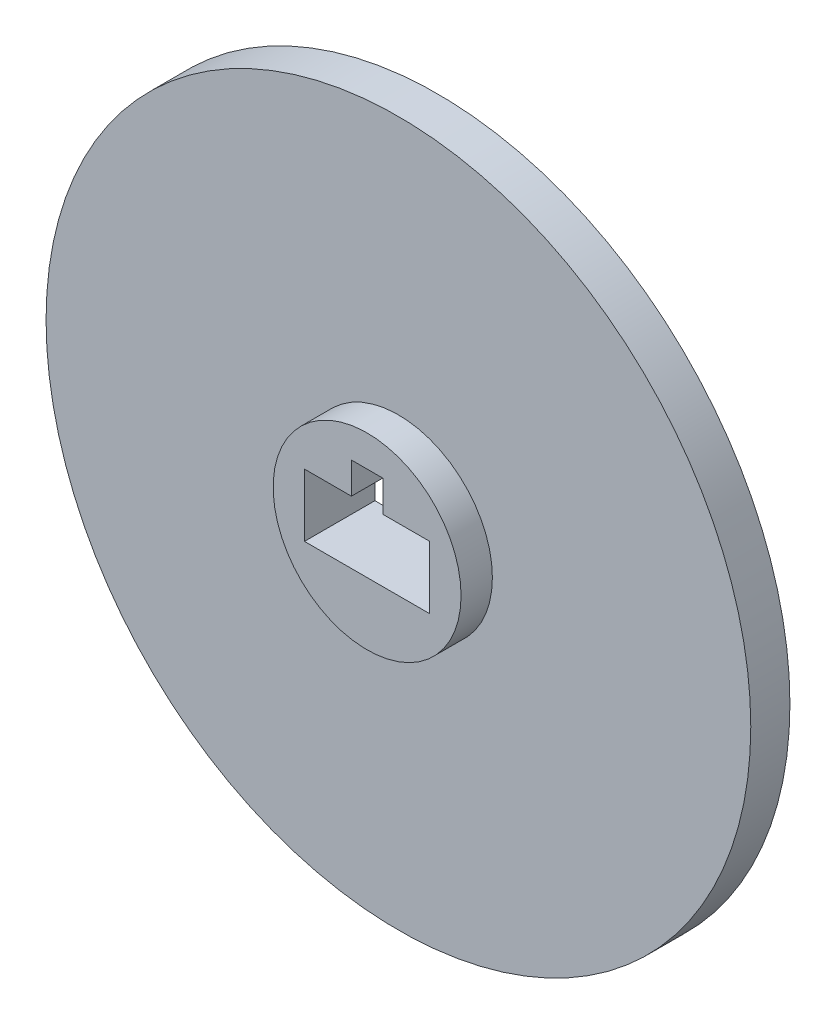
SolidWorks part; units mm, degrees
ref_plane "Front Plane" through (0, 0, 0) normal (0, 0, 1) x (1, 0, 0)
ref_plane "Top Plane" through (0, 0, 0) normal (0, 1, 0) x (1, 0, 0)
ref_plane "Right Plane" through (0, 0, 0) normal (1, 0, 0) x (0, 0, -1)
sketch "Sketch1" plane through (0, 0, 0) normal (0, 0, 1) x (1, 0, 0)
  circle A0 centre (0, 0) radius 22.5
  dimension "D1" = 45
extrude "Boss-Extrude1" add sketch "Sketch1" along normal blind 2.5
sketch "Sketch2" plane through (0, 0, 2.5) normal (0, 0, 1) x (1, 0, 0)
  circle A0 centre (0, 0) radius 6
  dimension "D1" = 12
extrude "Boss-Extrude2" add sketch "Sketch2" along normal blind 2
sketch "Sketch3" plane through (0, 0, 4.5) normal (0, 0, 1) x (1, 0, 0)
  line L0 (0, 0) -> (0, 6) construction
  line L1 (-4, 2) -> (4, 2) construction
  line L2 (-4, 2) -> (-4, -2)
  line L3 (-4, -2) -> (4, -2)
  line L4 (4, 2) -> (4, -2)
  line L5 (-4, 2) -> (4, -2) construction
  line L6 (-4, -2) -> (4, 2) construction
  line L7 (-4, 2) -> (-1, 2)
  line L8 (1, 4) -> (-1, 4)
  line L9 (1, 4) -> (1, 2)
  line L10 (1, 2) -> (-1, 2) construction
  line L11 (-1, 4) -> (-1, 2)
  line L12 (1, 4) -> (-1, 2) construction
  line L13 (1, 2) -> (-1, 4) construction
  line L14 (1, 2) -> (4, 2)
  circle A0 centre (0, 0) radius 6 construction
  point P0 (0, 0)
  point P10 (0, 3)
  dimension "D1" = 8
  dimension "D2" = 4
  dimension "D3" = 2
  dimension "D4" = 2
extrude "Cut-Extrude1" cut sketch "Sketch3" against normal blind 10
